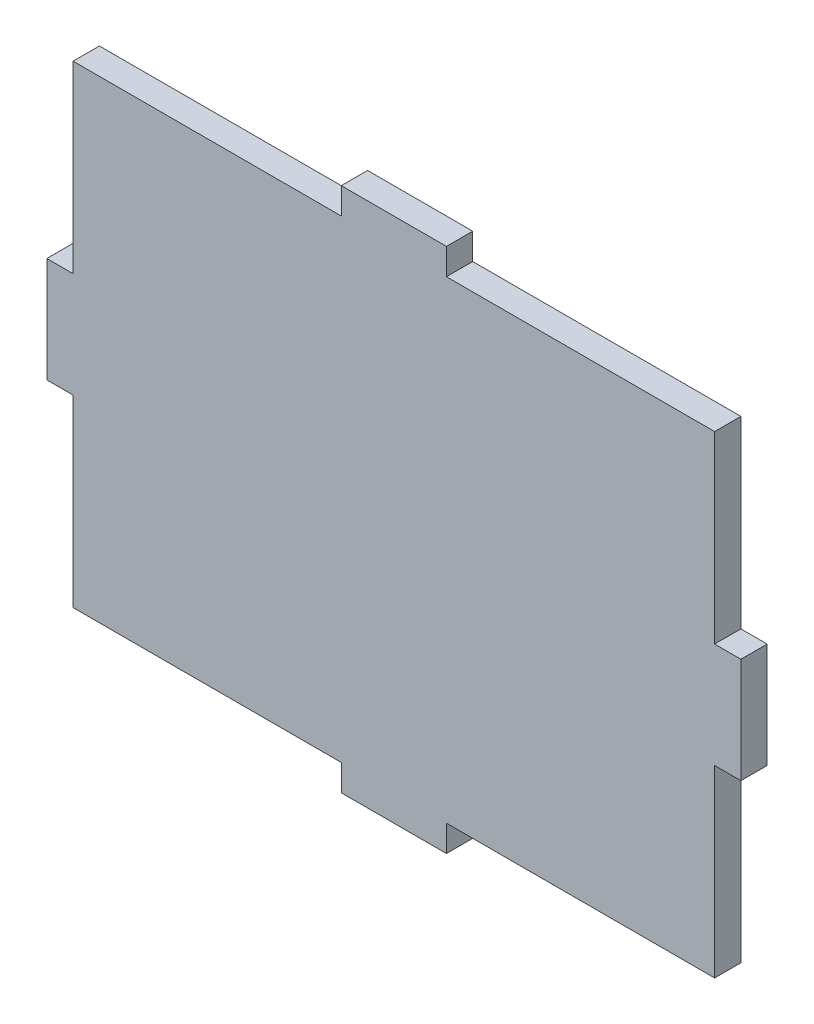
SolidWorks part; units mm, degrees
material "Acrylic (Medium-high impact)"
ref_plane "Front Plane" through (0, 0, 0) normal (0, 0, 1) x (1, 0, 0)
ref_plane "Top Plane" through (0, 0, 0) normal (0, 1, 0) x (1, 0, 0)
ref_plane "Right Plane" through (0, 0, 0) normal (1, 0, 0) x (0, 0, -1)
sketch "Sketch1" plane through (0, 0, 0) normal (0, 0, 1) x (1, 0, 0)
  line L0 (-38.735, 6.35) -> (-41.91, 6.35)
  line L1 (-38.735, -28.575) -> (-6.35, -28.575)
  line L2 (-38.735, -28.575) -> (-38.735, -6.35)
  line L3 (-38.735, 28.575) -> (-6.35, 28.575)
  line L4 (38.735, -28.575) -> (38.735, -6.35)
  line L5 (-38.735, -28.575) -> (38.735, 28.575) construction
  line L6 (-38.735, 28.575) -> (38.735, -28.575) construction
  line L7 (-41.91, 6.35) -> (-41.91, -6.35)
  line L8 (-41.91, -6.35) -> (-38.735, -6.35)
  line L9 (6.35, 28.575) -> (38.735, 28.575)
  line L10 (-6.35, 28.575) -> (-6.35, 31.75)
  line L11 (-6.35, 31.75) -> (6.35, 31.75)
  line L12 (6.35, 31.75) -> (6.35, 28.575)
  line L13 (38.735, 6.35) -> (38.735, 28.575)
  line L14 (38.735, 6.35) -> (41.91, 6.35)
  line L15 (41.91, 6.35) -> (41.91, -6.35)
  line L16 (41.91, -6.35) -> (38.735, -6.35)
  line L17 (-6.35, -28.575) -> (-6.35, -31.75)
  line L18 (-6.35, -31.75) -> (6.35, -31.75)
  line L19 (6.35, -31.75) -> (6.35, -28.575)
  line L20 (6.35, -28.575) -> (38.735, -28.575)
  line L21 (-38.735, 6.35) -> (-38.735, 28.575)
  point P0 (0, 0)
  dimension "D1" = 77.47
  dimension "D2" = 57.15
  dimension "D3" = 3.175
  dimension "D4" = 12.7
extrude "Boss-Extrude1" add sketch "Sketch1" along normal blind 3.175
